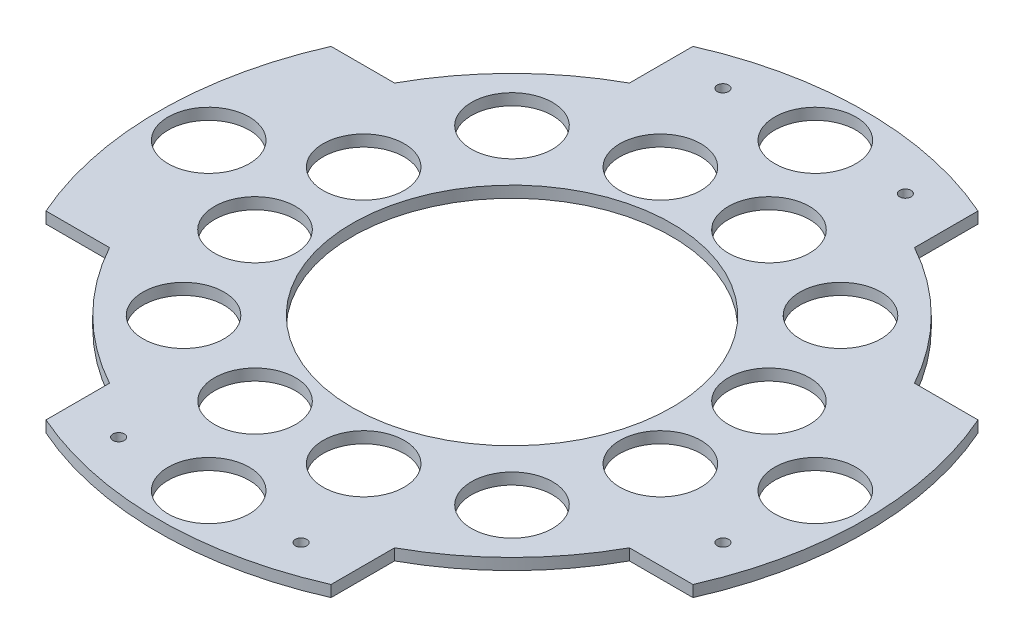
SolidWorks part; units mm, degrees
material "Custom Plastic"
ref_plane "Front Plane" through (0, 0, 0) normal (0, 0, 1) x (1, 0, 0)
ref_plane "Top Plane" through (0, 0, 0) normal (0, 1, 0) x (1, 0, 0)
ref_plane "Right Plane" through (0, 0, 0) normal (1, 0, 0) x (0, 0, -1)
sketch "Sketch1" plane through (0, 0, 0) normal (0, 1, 0) x (1, 0, 0)
  line L0 (-6.25, 14.1841) -> (-6.25, 11.399)
  line L1 (0, 15.5) -> (0, 0) construction
  line L2 (0, 0) -> (-10.9602, 10.9602) construction
  line L3 (-14.1841, 6.25) -> (-11.399, 6.25)
  line L4 (6.25, 14.1841) -> (6.25, 11.399)
  line L5 (14.1841, 6.25) -> (11.399, 6.25)
  line L6 (0, 0) -> (15.5, 0) construction
  line L7 (14.1841, -6.25) -> (11.399, -6.25)
  line L8 (6.25, -14.1841) -> (6.25, -11.399)
  line L9 (-6.25, -14.1841) -> (-6.25, -11.399)
  line L10 (-14.1841, -6.25) -> (-11.399, -6.25)
  circle A0 centre (0, 0) radius 13 construction
  circle A1 centre (0, 0) radius 15.5 construction
  arc A2 (-6.25, 14.1841) -> (6.25, 14.1841) centre (0, 0) cw
  arc A3 (-6.25, 11.399) -> (-11.399, 6.25) centre (0, 0) ccw
  arc A4 (-14.1841, 6.25) -> (-14.1841, -6.25) centre (0, 0) ccw
  arc A5 (6.25, 11.399) -> (11.399, 6.25) centre (0, 0) cw
  arc A6 (14.1841, 6.25) -> (14.1841, -6.25) centre (0, 0) cw
  arc A7 (6.25, -11.399) -> (11.399, -6.25) centre (0, 0) ccw
  arc A8 (-6.25, -14.1841) -> (6.25, -14.1841) centre (0, 0) ccw
  arc A9 (-6.25, -11.399) -> (-11.399, -6.25) centre (0, 0) cw
  circle A10 centre (0, 0) radius 7
  dimension "D1" = 31
  dimension "D2" = 26
  dimension "D5" = 14
  dimension "D3" = 6.25
  dimension "D4" = 45
extrude "Boss-Extrude1" add sketch "Sketch1" along normal blind 0.5
sketch "Sketch2" plane through (0, 0.5, 0) normal (0, 1, 0) x (1, 0, 0)
  line L0 (0, 0) -> (-15.5, 0) construction
  line L2 (-9.1924, 9.1924) -> (0, 0) construction
  line L4 (0, 0) -> (-14.9719, 4.0117) construction
  line L11 (0, 0) -> (0, 15.5) construction
  circle A0 centre (0, 13.3) radius 1.778
  circle A1 centre (-2.3811, 8.8865) radius 1.778
  arc A2 (-14.1841, 6.25) -> (-14.1841, -6.25) centre (0, 0) ccw construction
  circle A3 centre (0, 0) radius 7 construction
  arc A4 (-6.25, 11.399) -> (-11.399, 6.25) centre (0, 0) ccw construction
  circle A5 centre (-13.3, 0) radius 1.778
  circle A6 centre (-8.8865, 2.3811) radius 1.778
  circle A7 centre (-7.2019, 7.2019) radius 1.778
  circle A8 centre (0, -13.3) radius 1.778
  circle A9 centre (-2.3811, -8.8865) radius 1.778
  circle A10 centre (-7.2019, -7.2019) radius 1.778
  circle A11 centre (-8.8865, -2.3811) radius 1.778
  circle A12 centre (2.3811, 8.8865) radius 1.778
  circle A13 centre (7.2019, 7.2019) radius 1.778
  circle A14 centre (8.8865, 2.3811) radius 1.778
  arc A15 (6.25, 14.1841) -> (-6.25, 14.1841) centre (0, 0) ccw construction
  circle A16 centre (13.3, 0) radius 1.778
  arc A17 (11.399, 6.25) -> (11.399, -6.25) centre (0, 0) cw construction
  circle A18 centre (8.8865, -2.3811) radius 1.778
  circle A19 centre (7.2019, -7.2019) radius 1.778
  circle A20 centre (2.3811, -8.8865) radius 1.778
  arc A36 (-11.399, 6.25) -> (-11.399, -6.25) centre (0, 0) ccw construction
  point P0 (-13, 0)
  point P11 (-7, 0)
  point P19 (-4.9497, 4.9497)
  point P20 (-15.078, 0)
  point P24 (-7.5, 0)
  point P25 (-8.5, 0)
  point P28 (-8.4591, 8.4591)
  point P56 (-6.7615, 1.8117)
  point P94 (-7.1691, 1.921)
  dimension "D2" = 3.556
  dimension "padRadius" = 1.778
  dimension "D7" = 13.3
  dimension "D1" = 10.185
  dimension "D3" = 0.5
  dimension "D4" = 1
  dimension "D5" = 15
  dimension "D6" = 9.2
extrude "Cut-Extrude2" cut sketch "Sketch2" against normal through all
sketch "Sketch3" plane through (0, 0.5, 0) normal (0, 1, 0) x (1, 0, 0)
  line L0 (0, 0) -> (0, 15.5) construction
  line L1 (0, 0) -> (15.5, 0) construction
  line L2 (0, 0) -> (4, 13.25) construction
  line L3 (0, 0) -> (13.25, -4) construction
  circle A0 centre (-4, 13.25) radius 1
  arc A1 (6.25, 14.1841) -> (-6.25, 14.1841) centre (0, 0) ccw construction
  arc A2 (14.1841, -6.25) -> (14.1841, 6.25) centre (0, 0) ccw construction
  circle A3 centre (4, 13.25) radius 1
  circle A4 centre (4, -13.25) radius 1
  circle A5 centre (-4, -13.25) radius 1
  circle A6 centre (13.25, -4) radius 1
  dimension "D2" = 2
  dimension "D1" = 13.25
  dimension "D3" = 4
  dimension "D5" = 90
  dimension "D6" = 13.25
  dimension "D7" = 4
  dimension "D4" = 2
extrude "Cut-Extrude1" [suppressed] cut sketch "Sketch3" against normal through all
sketch "Sketch4" plane through (0, 0.5, 0) normal (0, 1, 0) x (1, 0, 0)
  circle A0 centre (4, 13.25) radius 1 construction
  circle A1 centre (-4, 13.25) radius 1 construction
  circle A2 centre (13.25, -4) radius 1 construction
  circle A3 centre (-4, -13.25) radius 1 construction
  circle A4 centre (4, -13.25) radius 1 construction
  circle A5 centre (4, 13.25) radius 1 construction
  circle A6 centre (-4, 13.25) radius 1 construction
  circle A7 centre (13.25, -4) radius 1 construction
  circle A8 centre (-4, -13.25) radius 1 construction
  circle A9 centre (4, -13.25) radius 1 construction
  circle A10 centre (-4, 13.25) radius 0.25
  circle A11 centre (13.25, -4) radius 0.25
  circle A12 centre (4, -13.25) radius 0.25
  circle A13 centre (-4, -13.25) radius 0.25
  circle A14 centre (4, 13.25) radius 0.25
  dimension "D1" = 0.5
  dimension "D2" = 0.5
  dimension "D3" = 0.5
  dimension "D4" = 0.5
  dimension "D5" = 0.5
extrude "Cut-Extrude3" cut sketch "Sketch4" against normal through all
equation "\"D2@Sketch2\" = \"padRadius\" * 2"
